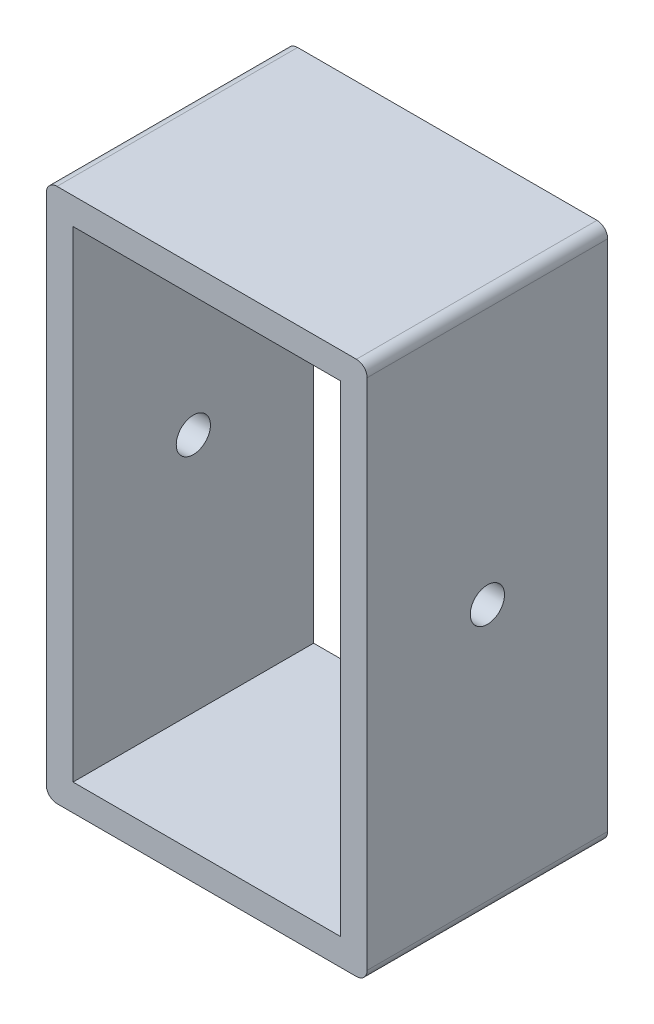
SolidWorks part; units mm, degrees
ref_plane "Front Plane" through (0, 0, 0) normal (0, 0, 1) x (1, 0, 0)
ref_plane "Top Plane" through (0, 0, 0) normal (0, 1, 0) x (1, 0, 0)
ref_plane "Right Plane" through (0, 0, 0) normal (1, 0, 0) x (0, 0, -1)
sketch "Sketch1" plane through (0, 0, 0) normal (1, 0, 0) x (0, 0, -1)
  line L1 (-11.25, -22.5) -> (11.25, -22.5)
  line L2 (-11.25, -22.5) -> (-11.25, 22.5)
  line L3 (-11.25, 22.5) -> (11.25, 22.5)
  line L4 (11.25, -22.5) -> (11.25, 22.5)
  line L5 (-11.25, -22.5) -> (11.25, 22.5) construction
  line L6 (-11.25, 22.5) -> (11.25, -22.5) construction
  point P0 (0, 0)
  dimension "D1" = 45
  dimension "D2" = 22.5
extrude "Boss-Extrude1" add sketch "Sketch1" along normal blind 2.5
ref_plane "Plane1" through (0, -22.5, 0) normal (0, -1, 0) x (-1, 0, 0)
sketch "Sketch2" plane through (0, -22.5, 0) normal (0, -1, 0) x (-1, 0, 0)
  line L1 (-2.5, 11.25) -> (25, 11.25)
  line L2 (-2.5, 11.25) -> (-2.5, -11.25)
  line L3 (-2.5, -11.25) -> (25, -11.25)
  line L4 (25, 11.25) -> (25, -11.25)
  dimension "D1" = 27.5
extrude "Boss-Extrude2" add sketch "Sketch2" along normal blind 2.5
ref_plane "Plane2" through (0, 22.5, 0) normal (0, 1, 0) x (1, 0, 0)
sketch "Sketch3" plane through (0, 22.5, 0) normal (0, 1, 0) x (1, 0, 0)
  line L1 (2.5, 11.25) -> (-25, 11.25)
  line L2 (2.5, 11.25) -> (2.5, -11.25)
  line L3 (2.5, -11.25) -> (-25, -11.25)
  line L4 (-25, 11.25) -> (-25, -11.25)
extrude "Boss-Extrude3" add sketch "Sketch3" along normal blind 2.5
ref_plane "Plane3" through (-25, 0, 0) normal (-1, 0, 0) x (0, 0, 1)
sketch "Sketch4" plane through (-25, 0, 0) normal (-1, 0, 0) x (0, 0, 1)
  line L1 (-11.25, 25) -> (11.25, 25)
  line L2 (-11.25, 25) -> (-11.25, -25)
  line L3 (-11.25, -25) -> (11.25, -25)
  line L4 (11.25, 25) -> (11.25, -25)
extrude "Boss-Extrude4" add sketch "Sketch4" along normal blind 2.5
ref_plane "Plane4" through (-27.5, 0, 0) normal (-1, 0, 0) x (0, 0, 1)
sketch "Sketch5" plane through (-27.5, 0, 0) normal (-1, 0, 0) x (0, 0, 1)
  circle A0 centre (0, 0) radius 1.6
  dimension "D1" = 3.2
extrude "Cut-Extrude1" cut sketch "Sketch5" against normal blind 30
fillet "Fillet2" radius 1 2 edges at (-27.5, 25, 0) (2.5, 25, 0)
fillet "Fillet3" radius 1 2 edges at (2.5, -25, 0) (-27.5, -25, 0)
